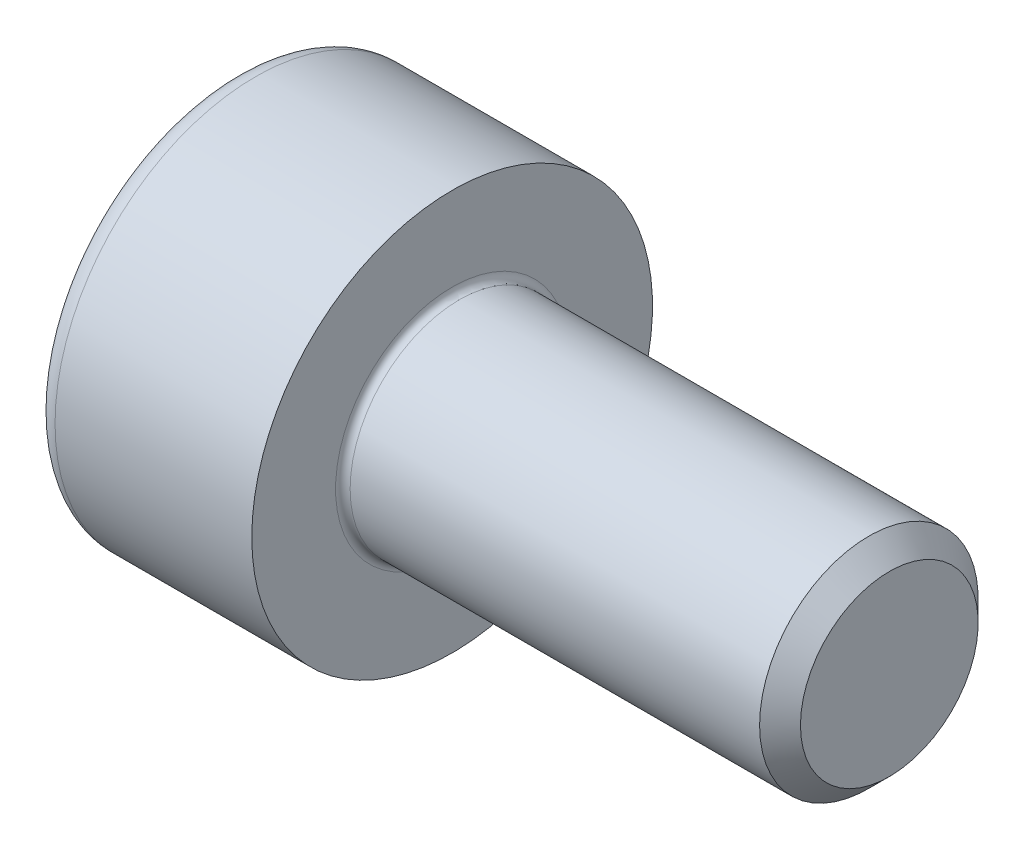
SolidWorks part; units mm, degrees
ref_plane "Plane1" through (0, 0, 0) normal (0, 0, 1) x (1, 0, 0)
ref_plane "Plane2" through (0, 0, 0) normal (0, 1, 0) x (1, 0, 0)
ref_plane "Plane3" through (0, 0, 0) normal (1, 0, 0) x (0, 0, -1)
sketch "BodySke" plane through (0, 0, 0) normal (0, 0, 1) x (1, 0, 0)
  line L0 (0, 0) -> (0, 2.75)
  line L1 (0, 2.75) -> (3, 2.75)
  line L2 (3, 2.75) -> (3, 1.5)
  line L3 (3, 1.5) -> (8.7195, 1.5)
  line L4 (9, 1.2195) -> (9, 0)
  line L5 (9, 0) -> (0, 0)
  line L6 (-31.75, 0) -> (127, 0) construction
  line L8 (9, 1.2195) -> (8.7195, 1.5)
  line L10 (9, -1.2195) -> (8.7195, -1.5) construction
  line L11 (3.5, 9.525) -> (3.5, 3.175) construction
  line L12 (3, 9.525) -> (3, 3.175) construction
  line L13 (-51, 9.525) -> (-51, 3.175) construction
  dimension "Diameter" = 3
  dimension "Head_ht" = 3
  dimension "Length" = 6
  dimension "Body_ch_ang" = 45
  dimension "Head_dia" = 5.5
  dimension "Minor_dia" = 2.439
  dimension "Advance" = 0.5
  dimension "Thread_nom" = 6
  dimension "Thread_length" = 60
revolve "Base-Revolve" add sketch "BodySke"
cosmetic thread "ThreadCosmetic"
fillet "Fillet1" radius 0.1 1 edges at (3, 0, 1.5)
fillet "Fillet2" radius 0.3 1 edges at (0, 0, 2.75)
sketch "Sketch2" plane through (0, 0, 0) normal (0, 0, 1) x (1, 0, 0)
  line L0 (0, 1.26) -> (1.3, 1.26)
  line L1 (1.3, 1.26) -> (2.0275, 0)
  line L2 (-31.75, 0) -> (127, 0) construction
  line L3 (2.0275, 0) -> (0, 0)
  line L4 (0, 0) -> (0, 1.26)
  line L6 (0, 0) -> (47.625, 0) construction
  dimension "D1" = 1.26
  dimension "D2" = 60
  dimension "Depth" = 1.3
revolve "Hex-PreBroach" cut sketch "Sketch2" angle 360 about L6
sketch "Sketch3" plane through (0, 0, 0) normal (-1, 0, 0) x (0, 0.5, 0.866)
  line L0 (0.7275, 1.26) -> (-0.7275, 1.26)
  line L1 (-0.7275, 1.26) -> (-1.4549, 0)
  line L2 (0.7275, 1.26) -> (1.4549, 0)
  line L3 (0.7275, -1.26) -> (1.4549, 0)
  line L4 (0.7275, -1.26) -> (-0.7275, -1.26)
  line L5 (-0.7275, -1.26) -> (-1.4549, 0)
  dimension "D1" = 1.26
  dimension "D2" = 1.26
  dimension "Hex_size" = 2.52
extrude "Hex" cut sketch "Sketch3" against normal blind 1.3
sketch "ThdSchSke" plane through (0, 0, 0) normal (0, 0, 1) x (1, 0, 0)
  line L0 (4.5, -1.2195) -> (4.3036, -1.5)
  line L1 (4.5, -1.2195) -> (4.6964, -1.5)
  line L2 (4.6964, -1.5) -> (4.6964, -1.875)
  line L3 (-3.175, 0) -> (5.1513, 0) construction
  line L4 (0, 2.45) -> (0, -2.45) construction
  line L5 (4.6964, -1.875) -> (4.3036, -1.875)
  line L6 (4.3036, -1.875) -> (4.3036, -1.5)
  dimension "Thread_minor" = 2.439
  dimension "Diameter" = 3
  dimension "Start" = 4.5
  dimension "SideAngle" = 55
  dimension "VeeAngle" = 70
  dimension "Overcut" = 3.75
revolve "ThreadSchematic" [suppressed] cut sketch "ThdSchSke" angle 360 about L3
pattern_linear "ThdSchPat" [suppressed]
equation "\"D2@Sketch3\" = \"Hex_size@Sketch3\" / 2"
equation "\"D1@Sketch3\" = \"Hex_size@Sketch3\" / 2"
equation "\"D1@Sketch2\" = \"Hex_size@Sketch3\" / 2"
equation "\"Thread_minor@ThreadCosmetic\"  =  \"Minor_dia@BodySke\""
equation "\"Depth@Sketch2\" =  \"Key_eng@Hex\""
equation "\"Thread_length@ThreadCosmetic\" = ((sgn( (\"Length@BodySke\" - \"Advance@BodySke\" * 3.0) - \"Thread_nom@BodySke\" )-1)*( (\"Length@BodySke\" - \"Advance@BodySke\" * 3.0) - \"Thread_nom@BodySke\" ))/-2+ \"Thread_nom@BodySke\""
equation "\"Thread_minor@ThdSchSke\" = \"Minor_dia@BodySke\""
equation "\"Diameter@ThdSchSke\" = \"Diameter@BodySke\""
equation "\"Overcut@ThdSchSke\" = \"Diameter@BodySke\" * 1.25"
equation "\"Start@ThdSchSke\" = \"Head_ht@BodySke\" + \"Length@BodySke\" - \"Thread_length@ThreadCosmetic\"  '---Non-countersunk---"
equation "\"Num_threads@ThdSchPat\" = int( \"Thread_length@ThreadCosmetic\" / \"Advance@BodySke\" + 0.999 )  + 1"
equation "\"Advance@ThdSchPat\" = \"Thread_length@ThreadCosmetic\" /  (\"Num_threads@ThdSchPat\" - 1) 'relax it"
equation "\"Num_threads@ThdSchPat\" = \"Num_threads@ThdSchPat\" - sgn( \"Num_threads@ThdSchPat\" - 1) '---chamfered tips only---"
